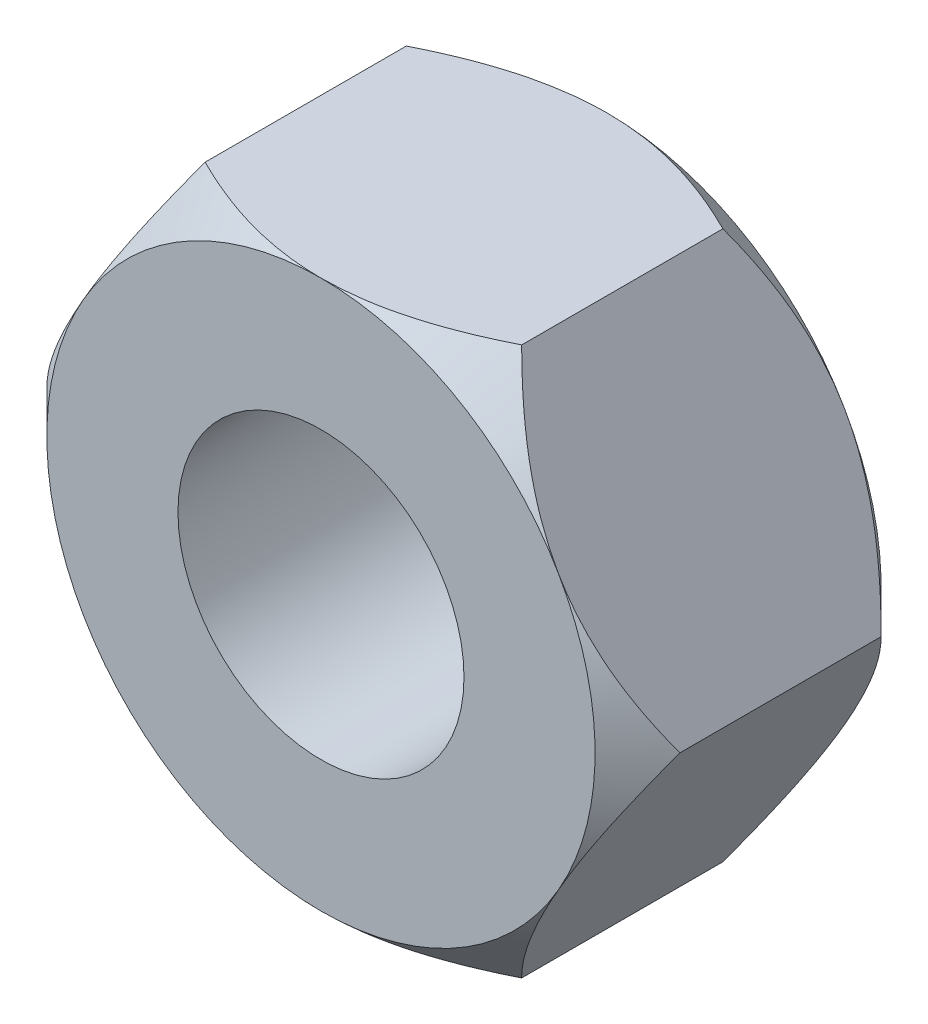
SolidWorks part; units mm, degrees
ref_plane "Front Plane" through (0, 0, 0) normal (0, 0, 1) x (1, 0, 0)
ref_plane "Top Plane" through (0, 0, 0) normal (0, 1, 0) x (1, 0, 0)
ref_plane "Right Plane" through (0, 0, 0) normal (1, 0, 0) x (0, 0, -1)
sketch "Sketch4" plane through (0, 0, 0) normal (0, 0, 1) x (1, 0, 0)
  line L1 (9.9593, 0) -> (4.9796, 8.625)
  line L2 (4.9796, 8.625) -> (-4.9796, 8.625)
  line L3 (-4.9796, 8.625) -> (-9.9593, 0)
  line L4 (-9.9593, 0) -> (-4.9796, -8.625)
  line L5 (-4.9796, -8.625) -> (4.9796, -8.625)
  line L6 (4.9796, -8.625) -> (9.9593, 0)
  circle A0 centre (0, 0) radius 8.625 construction
  circle A1 centre (0, 0) radius 4.5
  dimension "D1" = 17.25
extrude "Boss-Extrude2" add sketch "Sketch4" along normal mid plane 9
sketch "Sketch5" plane through (0, 0, 4.5) normal (0, 0, 1) x (1, 0, 0)
  circle A0 centre (0, 0) radius 8.625
extrude "Cut-Extrude2" cut sketch "Sketch5" against normal blind 9 draft 45 flip side to cut
mirror "Mirror1" about plane through (0, 0, 0) normal (0, 0, 1) of "Cut-Extrude2"
